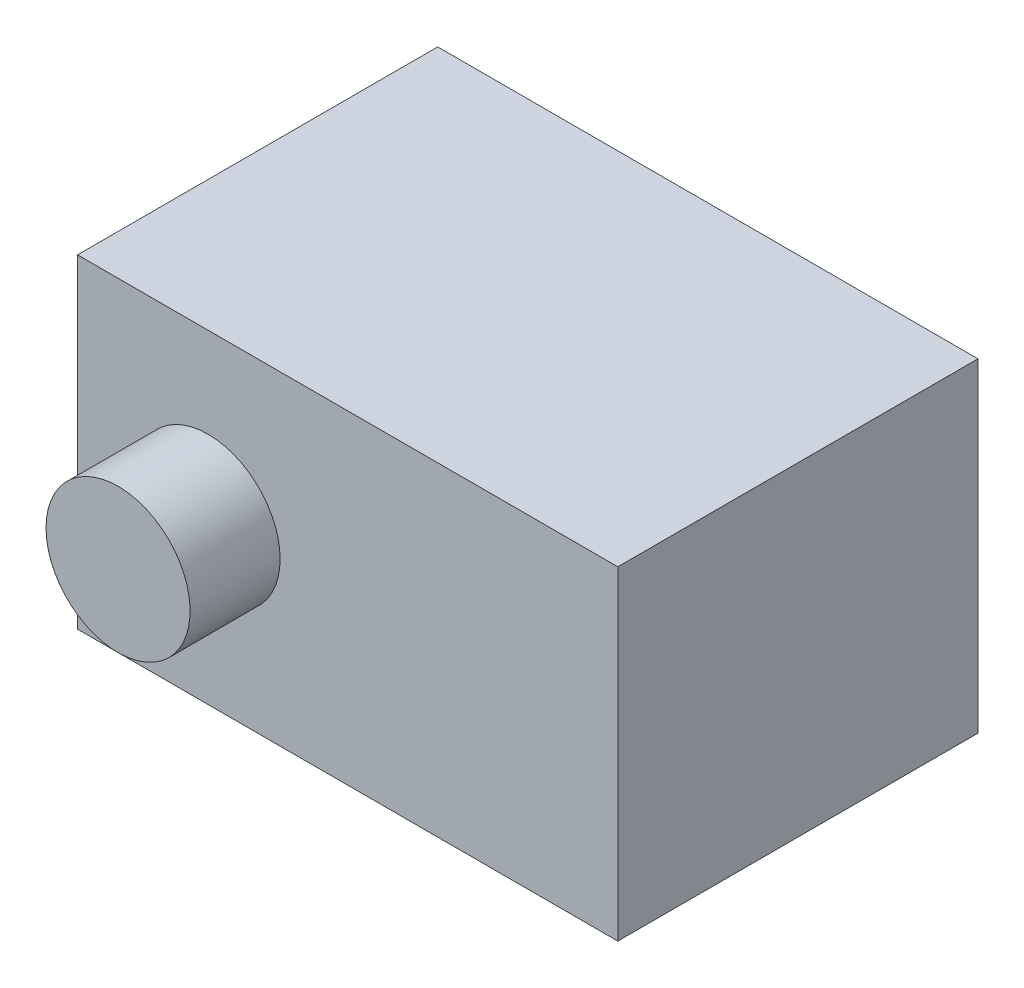
SolidWorks part; units mm, degrees
ref_plane "Plan de face" through (0, 0, 0) normal (0, 0, 1) x (1, 0, 0)
ref_plane "Plan de dessus" through (0, 0, 0) normal (0, 1, 0) x (1, 0, 0)
ref_plane "Plan de droite" through (0, 0, 0) normal (1, 0, 0) x (0, 0, -1)
sketch "Esquisse1" plane through (0, 0, 0) normal (0, 0, 1) x (1, 0, 0)
  line L1 (-15, 9) -> (15, 9)
  line L2 (-15, 9) -> (-15, -9)
  line L3 (-15, -9) -> (15, -9)
  line L4 (15, 9) -> (15, -9)
  line L5 (-15, 9) -> (15, -9) construction
  line L6 (-15, -9) -> (15, 9) construction
  point P0 (0, 0)
  dimension "D1" = 30
  dimension "D2" = 18
extrude "Boss.-Extru.1" add sketch "Esquisse1" along normal blind 20
sketch "Esquisse2" plane through (0, 0, 0) normal (0, 0, -1) x (-1, 0, 0)
  line L0 (15, 9) -> (15, -9) construction
  circle A0 centre (7.75, 0) radius 4
  dimension "D2" = 8
  dimension "D1" = 7.25
extrude "Boss.-Extru.2" add sketch "Esquisse2" along normal blind 5
ref_plane "Plan1" through (0, 0, 10) normal (0, 0, 1) x (1, 0, 0)
mirror "Symétrie1" about plane through (0, 0, 10) normal (0, 0, 1) of "Boss.-Extru.2"
